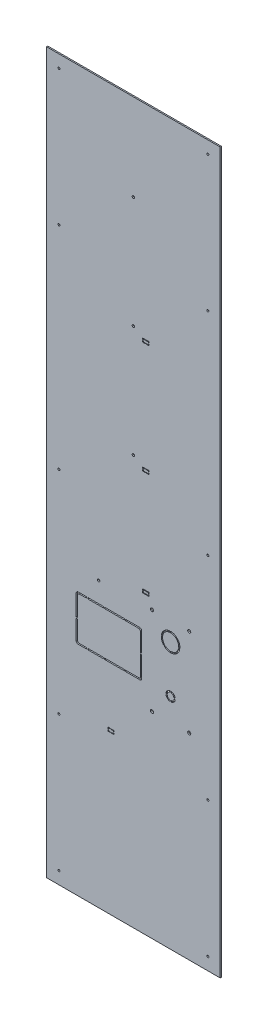
SolidWorks part; units mm, degrees
ref_plane "Front Plane" through (0, 0, 0) normal (0, 0, 1) x (1, 0, 0)
ref_plane "Top Plane" through (0, 0, 0) normal (0, 1, 0) x (1, 0, 0)
ref_plane "Right Plane" through (0, 0, 0) normal (1, 0, 0) x (0, 0, -1)
sketch "Sketch2" plane through (0, 0, 0) normal (0, 0, 1) x (1, 0, 0)
  line L0 (-140, -580) -> (-100, -580) construction
  line L5 (0, -480) -> (0, 680) construction
  line L6 (-140, 0) -> (140, 0) construction
  line L7 (-140, -580) -> (-100, -580) construction
  line L8 (140, -580) -> (84.8632, -580) construction
  line L9 (-100, -580) -> (-100, -777.353) construction
  line L10 (-100, -777.353) -> (-100, 757.3061) construction
  line L11 (100, -814.4523) -> (100, 771.4404) construction
  line L12 (-140, 680) -> (-140, 150) construction
  line L14 (-140, 680) -> (140, 680)
  line L15 (140, 680) -> (140, 580)
  line L16 (0, -580) -> (0, -480) construction
  line L17 (-140, -480) -> (140, -480)
  line L19 (140, -480) -> (140, 580)
  line L20 (-140, -480) -> (-140, 680)
  line L21 (-140, 150) -> (140, 150) construction
  line L22 (140, 150) -> (140, 110) construction
  line L23 (140, 110) -> (-140, 110) construction
  point P0 (0, 0)
  dimension "D2" = 280
extrude "Boss-Extrude2" add sketch "Sketch2" along normal blind 2
sketch "Sketch3" plane through (0, 0, 0) normal (0, 0, 1) x (1, 0, 0)
  line L0 (120, 660) -> (120, 441.5) construction
  line L1 (-48.3697, -128.55) -> (-48.3697, -126.55)
  line L2 (-140, 660) -> (-120, 660) construction
  line L3 (120, 441.5) -> (-120, 441.5) construction
  line L4 (-120, 660) -> (-120, 680) construction
  line L5 (120, -460) -> (120, 100) construction
  line L6 (120, 100) -> (-120, 100) construction
  line L7 (-120, 680) -> (-120, 150) construction
  line L8 (-198.9172, 110) -> (186.996, 110) construction
  line L9 (-140, -480) -> (-100, -480) construction
  line L10 (60, -163) -> (90, -163) construction
  line L11 (0, 360) -> (0, 348) construction
  line L12 (-198.9172, 150) -> (186.996, 150) construction
  line L13 (0, 348) -> (20, 348) construction
  line L14 (186.996, 150) -> (186.996, 110) construction
  line L16 (60, -163) -> (30, -163) construction
  line L17 (-56.1, -21) -> (-56.1, -23) construction
  line L20 (-140, 680) -> (140, 680) construction
  line L21 (13.4823, -92.0553) -> (11.4823, -92.0553)
  line L23 (140, 660) -> (120, 660) construction
  line L24 (-56.1, 150) -> (-56.1, 110) construction
  line L25 (60, -21) -> (60, -36) construction
  line L26 (60, 0) -> (60, -21) construction
  line L27 (60, -21) -> (90, -21) construction
  line L28 (60, -127) -> (60, -163) construction
  line L29 (90, -163) -> (90, -21) construction
  line L30 (30, -163) -> (30, -21) construction
  line L31 (30, -21) -> (60, -21) construction
  line L127 (-140, 680) -> (-140, 640) construction
  line L132 (60, -36) -> (60, -38)
  line L137 (59.0006, -36.0333) -> (59.1224, -38.0297)
  line L222 (59.958, -51.042) -> (70.6066, -40.3934) construction
  line L223 (59.958, -51.042) -> (70.5575, -61.6415) construction
  line L224 (60, -51) -> (50.8076, -41.8076) construction
  line L225 (59.958, -51.042) -> (49.3934, -61.6066) construction
  line L230 (74.9337, -52.4092) -> (72.9425, -52.2213)
  line L231 (74.8066, -53.4011) -> (72.8324, -53.0809)
  line L232 (60, -66) -> (60, -64)
  line L233 (59.0005, -65.9671) -> (59.0005, -63.9615)
  line L250 (67.5, -127) -> (52.5, -127) construction
  line L251 (60, -127) -> (60, -119.5) construction
  line L252 (60, -119.5) -> (60, -121.5) construction
  line L253 (67.5, -127) -> (65.5, -127) construction
  line L254 (65.5, -127) -> (60, -127) construction
  line L255 (60, -127) -> (60, -132.5) construction
  line L256 (60, -127) -> (54.6967, -121.6967) construction
  line L257 (60, -127) -> (65.3033, -132.3033) construction
  line L258 (60, -127) -> (54.6967, -132.3033) construction
  line L259 (60, -127) -> (65.3033, -121.6967) construction
  line L260 (60.9806, -119.5644) -> (60.7191, -121.5472)
  line L261 (67.4356, -126.0194) -> (65.4528, -126.2809)
  line L262 (58.9874, -119.5687) -> (59.2574, -121.5504)
  line L263 (67.4356, -127.9806) -> (65.4528, -127.7191)
  line L264 (52.5644, -126.0194) -> (54.5472, -126.2809)
  line L265 (52.5644, -127.9806) -> (54.5472, -127.7191)
  line L266 (58.9874, -134.4313) -> (59.2574, -132.4496)
  line L267 (60.9806, -134.4356) -> (60.7191, -132.4528)
  line L268 (45.2633, -48.202) -> (47.2282, -48.5751)
  line L269 (45.1082, -49.202) -> (47.0937, -49.4417)
  line L270 (49.0202, -40.7803) -> (50.4841, -42.1429)
  line L271 (48.3636, -41.5346) -> (49.9151, -42.7966)
  line L272 (48.3636, -60.4655) -> (49.9151, -59.2034)
  line L273 (49.3934, -61.6066) -> (50.8076, -60.1924)
  line L274 (69.988, -62.191) -> (68.6563, -60.6989)
  line L275 (69.2202, -62.8317) -> (67.9908, -61.2541)
  line L276 (69.5589, -39.4403) -> (68.2844, -40.9816)
  line L277 (70.3079, -40.1029) -> (68.9335, -41.5558)
  line L295 (-32.1, -221.1) -> (-35.6, -221.1)
  line L302 (24, 349.9) -> (20.5, 349.9)
  line L304 (120, -460) -> (120, -241.5) construction
  line L305 (120, -241.5) -> (-120, -241.5) construction
  line L306 (100, 784.4571) -> (100, -643.8463) construction
  line L308 (0, 540) -> (0, 640) construction
  line L310 (-92.1294, -91.8797) -> (-92.1294, -93.8797) construction
  line L311 (-140, 640) -> (140, 640) construction
  line L314 (-140, -480) -> (-140, -440) construction
  line L315 (-140, -440) -> (140, -440) construction
  line L316 (-14.4791, -57.5605) -> (-14.4791, -55.5605)
  line L319 (-12.4791, -55.5605) -> (-12.4791, -57.5605)
  line L320 (-100, -480) -> (-100, 680) construction
  line L328 (-92.1294, -93.8797) -> (-90.1294, -93.8797)
  line L329 (-90.1294, -91.8797) -> (-92.1294, -91.8797)
  line L334 (-90.1294, -123.55) -> (-90.1294, -93.8797)
  line L335 (-92.1294, -93.8797) -> (-92.1294, -125.55)
  line L336 (-92.1294, -91.8797) -> (-92.1294, -58.5605)
  line L337 (-90.1294, -60.5605) -> (-90.1294, -91.8797)
  line L338 (-120, -480) -> (-120, -460) construction
  line L339 (-120, -460) -> (-140, -460) construction
  line L340 (13.4823, -90.0553) -> (13.4823, -92.0553) construction
  line L341 (120, -480) -> (120, -460) construction
  line L342 (-14.4791, -126.55) -> (-14.4791, -128.55)
  line L343 (-12.4791, -126.55) -> (-12.4791, -128.55)
  line L344 (-75.4282, -128.55) -> (-75.4282, -126.55)
  line L345 (-75.906, -57.5605) -> (-75.906, -55.5605)
  line L346 (-73.4282, -128.55) -> (-73.4282, -126.55)
  line L347 (-73.4282, -57.5605) -> (-73.4282, -55.5605)
  line L348 (-48.3697, -57.5605) -> (-48.3697, -55.5605)
  line L349 (-46.3697, -128.55) -> (-46.3697, -126.55)
  line L350 (-46.3697, -57.5605) -> (-46.3697, -55.5605)
  line L351 (11.4823, -90.0553) -> (13.4823, -90.0553)
  line L352 (11.4823, -123.55) -> (11.4823, -92.0553)
  line L353 (11.4823, -90.0553) -> (11.4823, -60.5605)
  line L354 (13.4823, -90.0553) -> (13.4823, -58.5605)
  line L355 (13.4823, -92.0553) -> (13.4823, -125.55)
  line L356 (-12.4791, -126.55) -> (8.4823, -126.55)
  line L357 (-12.4791, -128.55) -> (10.4823, -128.55)
  line L358 (-12.4791, -57.5605) -> (8.4823, -57.5605)
  line L359 (-12.4791, -55.5605) -> (10.4823, -55.5605)
  line L360 (-46.3697, -55.5605) -> (-14.4791, -55.5605)
  line L361 (-14.4791, -57.5605) -> (-46.3697, -57.5605)
  line L362 (-46.3697, -128.55) -> (-14.4791, -128.55)
  line L363 (-14.4791, -126.55) -> (-46.3697, -126.55)
  line L364 (-73.4282, -128.55) -> (-48.3697, -128.55)
  line L365 (-48.3697, -126.55) -> (-73.4282, -126.55)
  line L366 (-73.4282, -57.5605) -> (-48.3697, -57.5605)
  line L367 (-48.3697, -55.5605) -> (-73.4282, -55.5605)
  line L368 (-87.1294, -57.5605) -> (-75.906, -57.5605)
  line L369 (-89.1294, -55.5605) -> (-75.906, -55.5605)
  line L370 (-89.1294, -128.55) -> (-75.4282, -128.55)
  line L371 (-75.4282, -126.55) -> (-87.1294, -126.55)
  line L372 (120, -460) -> (140, -460) construction
  line L373 (13.4823, -91.0553) -> (-92.1294, -91.0553) construction
  line L374 (140, 680) -> (140, 580) construction
  line L375 (120, 660) -> (120, 680) construction
  line L388 (25, 350.9) -> (20.5, 350.9)
  line L421 (20, 165.1) -> (20, 170.9) construction
  line L423 (25, 168) -> (15, 168) construction
  line L430 (20, 168) -> (20, -2) construction
  line L433 (20, 11.28) -> (20, 17.08) construction
  line L438 (0, 540) -> (0, 360) construction
  line L439 (0, -480) -> (0, 680) construction
  line L457 (20, -4.9) -> (20, 0.9) construction
  line L459 (25, -2) -> (15, -2) construction
  line L473 (25, 350.9) -> (25, 348.5)
  line L475 (25, 345.1) -> (20.5, 345.1)
  line L476 (15, 350.9) -> (15, 348.5)
  line L478 (20, 345.1) -> (20, 350.9) construction
  line L479 (25, 348) -> (15, 348) construction
  line L481 (16, 349.9) -> (16, 348.5)
  line L482 (24, 346.1) -> (20.5, 346.1)
  line L484 (24, 349.9) -> (24, 348.5)
  line L485 (0, 180) -> (0, 168) construction
  line L486 (0, 168) -> (20, 168) construction
  line L497 (24, 169.9) -> (24, 168.5)
  line L499 (25, 170.9) -> (20.5, 170.9)
  line L500 (25, 170.9) -> (25, 168.5)
  line L502 (25, 165.1) -> (20.5, 165.1)
  line L504 (15, 170.9) -> (15, 168.5)
  line L506 (20, 165.1) -> (20, 170.9) construction
  line L508 (25, 168) -> (15, 168) construction
  line L509 (24, 166.1) -> (20.5, 166.1)
  line L511 (-40.1, -221.1) -> (-40.1, -222.5)
  line L521 (24, -0.1) -> (20.5, -0.1)
  line L523 (25, 0.9) -> (20.5, 0.9)
  line L525 (25, 0.9) -> (25, -1.5)
  line L527 (25, -4.9) -> (20.5, -4.9)
  line L528 (15, 0.9) -> (15, -1.5)
  line L530 (20, -4.9) -> (20, 0.9) construction
  line L532 (25, -2) -> (15, -2) construction
  line L534 (16, -0.1) -> (16, -1.5)
  line L535 (-31.1, -220.1) -> (-35.6, -220.1)
  line L536 (-31.1, -220.1) -> (-31.1, -222.5)
  line L537 (16, 169.9) -> (16, 168.5)
  line L538 (24, 169.9) -> (20.5, 169.9)
  line L539 (25, 348.5) -> (24, 348.5)
  line L540 (25, 347.5) -> (24, 347.5)
  line L541 (19.5, 346.1) -> (16, 346.1)
  line L542 (25, 347.5) -> (25, 345.1)
  line L543 (20.5, 350.9) -> (20.5, 349.9)
  line L544 (19.5, 350.9) -> (19.5, 349.9)
  line L545 (20.5, 346.1) -> (20.5, 345.1)
  line L546 (19.5, 346.1) -> (19.5, 345.1)
  line L547 (16, 348.5) -> (15, 348.5)
  line L548 (16, 347.5) -> (15, 347.5)
  line L549 (19.5, 350.9) -> (15, 350.9)
  line L550 (25, 350.9) -> (15, 350.9) construction
  line L551 (19.5, 349.9) -> (16, 349.9)
  line L552 (24, 349.9) -> (16, 349.9) construction
  line L553 (24, 346.1) -> (16, 346.1) construction
  line L554 (19.5, 345.1) -> (15, 345.1)
  line L555 (25, 345.1) -> (15, 345.1) construction
  line L556 (16, 347.5) -> (16, 346.1)
  line L557 (16, 349.9) -> (16, 346.1) construction
  line L558 (15, 347.5) -> (15, 345.1)
  line L559 (15, 350.9) -> (15, 345.1) construction
  line L560 (25, 350.9) -> (25, 345.1) construction
  line L561 (24, 347.5) -> (24, 346.1)
  line L562 (24, 349.9) -> (24, 346.1) construction
  line L563 (19.5, 165.1) -> (15, 165.1)
  line L564 (19.5, 169.9) -> (16, 169.9)
  line L565 (16, 167.5) -> (16, 166.1)
  line L566 (24, -3.9) -> (20.5, -3.9)
  line L567 (25, 168.5) -> (24, 168.5)
  line L568 (25, 167.5) -> (24, 167.5)
  line L569 (16, 168.5) -> (15, 168.5)
  line L570 (16, 167.5) -> (15, 167.5)
  line L571 (20.5, 170.9) -> (20.5, 169.9)
  line L572 (19.5, 170.9) -> (19.5, 169.9)
  line L573 (20.5, 166.1) -> (20.5, 165.1)
  line L574 (19.5, 166.1) -> (19.5, 165.1)
  line L575 (25, 167.5) -> (25, 165.1)
  line L576 (25, 170.9) -> (25, 165.1) construction
  line L577 (24, 167.5) -> (24, 166.1)
  line L578 (24, 169.9) -> (24, 166.1) construction
  line L579 (25, 165.1) -> (15, 165.1) construction
  line L580 (19.5, 166.1) -> (16, 166.1)
  line L581 (24, 166.1) -> (16, 166.1) construction
  line L582 (19.5, 170.9) -> (15, 170.9)
  line L583 (25, 170.9) -> (15, 170.9) construction
  line L584 (24, 169.9) -> (16, 169.9) construction
  line L585 (16, 169.9) -> (16, 166.1) construction
  line L586 (15, 167.5) -> (15, 165.1)
  line L587 (15, 170.9) -> (15, 165.1) construction
  line L588 (24, -0.1) -> (24, -1.5)
  line L589 (-31.1, -225.9) -> (-35.6, -225.9)
  line L590 (-41.1, -220.1) -> (-41.1, -222.5)
  line L591 (25, -2.5) -> (24, -2.5)
  line L592 (25, -1.5) -> (24, -1.5)
  line L593 (24, -2.5) -> (24, -3.9)
  line L594 (20.5, 0.9) -> (20.5, -0.1)
  line L595 (19.5, 0.9) -> (19.5, -0.1)
  line L596 (20.5, -3.9) -> (20.5, -4.9)
  line L597 (19.5, -3.9) -> (19.5, -4.9)
  line L598 (16, -1.5) -> (15, -1.5)
  line L599 (16, -2.5) -> (15, -2.5)
  line L600 (19.5, 0.9) -> (15, 0.9)
  line L601 (25, 0.9) -> (15, 0.9) construction
  line L602 (19.5, -0.1) -> (16, -0.1)
  line L603 (24, -0.1) -> (16, -0.1) construction
  line L604 (19.5, -3.9) -> (16, -3.9)
  line L605 (24, -3.9) -> (16, -3.9) construction
  line L606 (19.5, -4.9) -> (15, -4.9)
  line L607 (25, -4.9) -> (15, -4.9) construction
  line L608 (15, -2.5) -> (15, -4.9)
  line L609 (15, 0.9) -> (15, -4.9) construction
  line L610 (16, -2.5) -> (16, -3.9)
  line L611 (16, -0.1) -> (16, -3.9) construction
  line L612 (25, -2.5) -> (25, -4.9)
  line L613 (25, 0.9) -> (25, -4.9) construction
  line L614 (24, -0.1) -> (24, -3.9) construction
  line L615 (-36.1, -224.9) -> (-36.1, -220.1) construction
  line L616 (-31.1, -223) -> (-41.1, -223) construction
  line L617 (-32.1, -224.9) -> (-35.6, -224.9)
  line L618 (-32.1, -221.1) -> (-32.1, -222.5)
  line L619 (-40.1, -223.5) -> (-40.1, -224.9)
  line L621 (-36.6, -224.9) -> (-40.1, -224.9)
  line L622 (-32.1, -223.5) -> (-32.1, -224.9)
  line L623 (-31.1, -223.5) -> (-32.1, -223.5)
  line L624 (-31.1, -222.5) -> (-32.1, -222.5)
  line L625 (-35.6, -220.1) -> (-35.6, -221.1)
  line L626 (-36.6, -220.1) -> (-36.6, -221.1)
  line L627 (-35.6, -224.9) -> (-35.6, -225.9)
  line L628 (-36.6, -224.9) -> (-36.6, -225.9)
  line L629 (-40.1, -222.5) -> (-41.1, -222.5)
  line L630 (-40.1, -223.5) -> (-41.1, -223.5)
  line L631 (-36.6, -220.1) -> (-41.1, -220.1)
  line L632 (-31.1, -220.1) -> (-41.1, -220.1) construction
  line L633 (-36.6, -221.1) -> (-40.1, -221.1)
  line L634 (-32.1, -221.1) -> (-40.1, -221.1) construction
  line L635 (-32.1, -224.9) -> (-40.1, -224.9) construction
  line L636 (-36.6, -225.9) -> (-41.1, -225.9)
  line L637 (-31.1, -225.9) -> (-41.1, -225.9) construction
  line L638 (-31.1, -223.5) -> (-31.1, -225.9)
  line L639 (-31.1, -220.1) -> (-31.1, -225.9) construction
  line L640 (-32.1, -221.1) -> (-32.1, -224.9) construction
  line L641 (-40.1, -221.1) -> (-40.1, -224.9) construction
  line L642 (-41.1, -223.5) -> (-41.1, -225.9)
  line L643 (-41.1, -220.1) -> (-41.1, -225.9) construction
  circle A20 centre (0, 540) radius 2
  circle A27 centre (-56.1, -23) radius 2
  arc A80 (60.9806, -119.5644) -> (67.4356, -126.0194) centre (60, -127) cw
  arc A96 (67.4356, -127.9806) -> (60.9806, -134.4356) centre (60, -127) cw
  arc A99 (58.9874, -134.4313) -> (52.5644, -127.9806) centre (60, -127) cw
  arc A108 (8.4823, -126.55) -> (11.4823, -123.55) centre (8.4823, -123.55) ccw
  arc A109 (58.9874, -119.5687) -> (52.5644, -126.0194) centre (60, -127) ccw
  arc A110 (60.7191, -121.5472) -> (65.4528, -126.2809) centre (60, -127) cw
  arc A111 (65.4528, -127.7191) -> (60.7191, -132.4528) centre (60, -127) cw
  arc A112 (59.2574, -132.4496) -> (54.5472, -127.7191) centre (60, -127) cw
  arc A113 (54.5472, -126.2809) -> (59.2574, -121.5504) centre (60, -127) cw
  arc A114 (13.4823, -125.55) -> (10.4823, -128.55) centre (10.4823, -125.55) cw
  arc A115 (10.4823, -55.5605) -> (13.4823, -58.5605) centre (10.4823, -58.5605) cw
  arc A116 (8.4823, -57.5605) -> (11.4823, -60.5605) centre (8.4823, -60.5605) cw
  arc A117 (-89.1294, -55.5605) -> (-92.1294, -58.5605) centre (-89.1294, -58.5605) ccw
  arc A118 (-90.1294, -60.5605) -> (-87.1294, -57.5605) centre (-87.1294, -60.5605) cw
  arc A119 (-92.1294, -125.55) -> (-89.1294, -128.55) centre (-89.1294, -125.55) ccw
  arc A120 (-87.1294, -126.55) -> (-90.1294, -123.55) centre (-87.1294, -123.55) cw
  arc A121 (70.3079, -40.1029) -> (74.9337, -52.4092) centre (60, -51) cw
  circle A122 centre (-120, -460) radius 1.65
  arc A123 (68.9335, -41.5558) -> (72.9425, -52.2213) centre (60, -51) cw
  arc A124 (72.8324, -53.0809) -> (68.6563, -60.6989) centre (60, -51) cw
  arc A125 (74.8066, -53.4011) -> (69.988, -62.191) centre (60, -51) cw
  arc A126 (69.2202, -62.8317) -> (60, -66) centre (60, -51) cw
  arc A127 (67.9908, -61.2541) -> (60, -64) centre (60, -51) cw
  arc A128 (59.0005, -63.9615) -> (50.8076, -60.1924) centre (60, -51) cw
  arc A129 (59.0005, -65.9671) -> (49.3934, -61.6066) centre (60.0005, -51.0005) cw
  arc A130 (49.9151, -59.2034) -> (47.0937, -49.4417) centre (60, -51) cw
  arc A131 (48.3636, -60.4655) -> (45.1082, -49.202) centre (60, -51) cw
  arc A132 (47.2282, -48.5751) -> (49.9151, -42.7966) centre (60, -51) cw
  arc A133 (45.2633, -48.202) -> (48.3636, -41.5346) centre (60, -51) cw
  arc A134 (50.4841, -42.1429) -> (59.1224, -38.0297) centre (60, -51) cw
  arc A135 (59.0006, -36.0333) -> (49.0202, -40.7803) centre (60, -51) ccw
  arc A136 (60, -36) -> (69.5589, -39.4403) centre (60, -51) cw
  arc A137 (60, -38) -> (68.2844, -40.9816) centre (60, -51) cw
  circle A138 centre (120, -460) radius 1.65
  circle A140 centre (90, -21) radius 2.5
  circle A141 centre (90, -163) radius 2.5
  circle A142 centre (30, -163) radius 2.5
  circle A143 centre (30, -21) radius 2.5
  circle A144 centre (-120, 660) radius 1.65
  circle A145 centre (120, 660) radius 1.65
  circle A146 centre (-120, 441.5) radius 1.65
  circle A147 centre (120, 441.5) radius 1.65
  circle A152 centre (120, -241.5) radius 1.65
  circle A153 centre (-120, -241.5) radius 1.65
  circle A154 centre (120, 100) radius 1.65
  circle A155 centre (-120, 100) radius 1.65
  circle A156 centre (0, 360) radius 2
  circle A157 centre (0, 180) radius 2
  point P126 (-36.1, -223)
  point P228 (-12.4791, -56.5605)
  point P251 (60, -51)
  point P346 (-73.4282, -127.55)
  point P349 (-91.1294, -91.8797)
  point P356 (-46.3697, -56.5605)
  point P357 (-46.3697, -127.55)
  dimension "D2" = 4
  dimension "D8" = 2
  dimension "D9" = 530
  dimension "D10" = 3.3
  dimension "D11" = 3
  dimension "D12" = 2
  dimension "D13" = 2
  dimension "D14" = 5
  dimension "D15" = 15
  dimension "D16" = 21
  dimension "D17" = 5
  dimension "D18" = 2
  dimension "D19" = 5
  dimension "D20" = 2
  dimension "D21" = 4
  dimension "D24" = 4
  dimension "D25" = 4
  dimension "D37" = 7.8706
  dimension "D44" = 1
  dimension "D39" = 218.5
  dimension "D40" = 5.8
  dimension "D49" = 20
  dimension "D53" = 5.8
  dimension "D57" = 10
  dimension "D62" = 1
  dimension "D54" = 45
  dimension "D56" = 45
  dimension "D55" = 1
  dimension "D48" = 1
  dimension "D68" = 1
  dimension "D30" = 3.3
  dimension "D31" = 3.3
  dimension "D46" = 10
  dimension "D36" = 5
  dimension "D26" = 3.3
  dimension "D27" = 3.3
  dimension "D28" = 3.3
  dimension "D22" = 170
  dimension "D23" = 3.3
  dimension "D32" = 3.3
  dimension "D33" = 3.3
  dimension "D41" = 3.3
  dimension "D29" = 2
  dimension "D34" = 40
  dimension "D35" = 20
  dimension "D38" = 5.8
  dimension "D42" = 10
  dimension "D43" = 10
  dimension "D45" = 5.8
  dimension "D47" = 1
  dimension "D50" = 1
  dimension "D51" = 1
  dimension "D52" = 1
  dimension "D70" = 1
  dimension "D71" = 1
extrude "Cut-Extrude8" cut sketch "Sketch3" along normal blind 2
sketch "Sketch4" plane through (0, 0, 0) normal (0, 0, 1) x (1, 0, 0)
  line L0 (-122.1114, -444.2649) -> (117.8886, -444.2649) construction
  text T0 "<b>HADIR</b>" font "Century Gothic" height in points 36
extrude "Cut-Extrude2" cut sketch "Sketch4" against normal blind 2 and the other way blind 0.1
